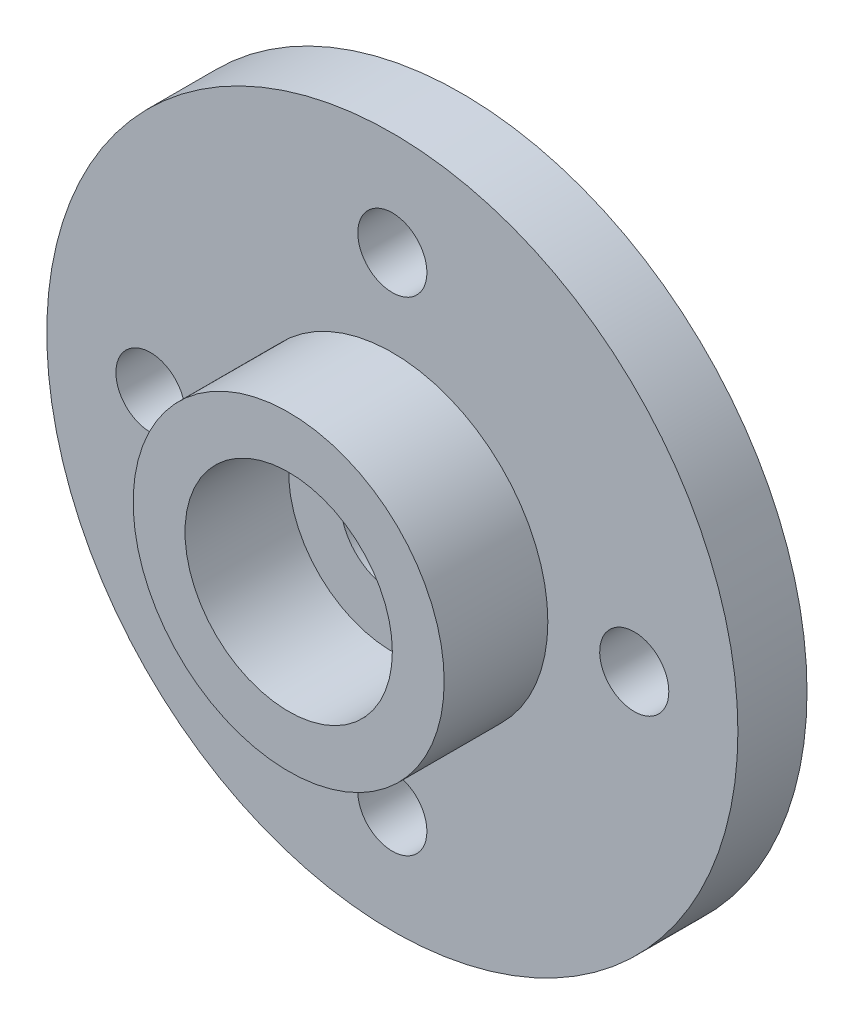
SolidWorks part; units mm, degrees
ref_plane "Front Plane" through (0, 0, 0) normal (0, 0, 1) x (1, 0, 0)
ref_plane "Top Plane" through (0, 0, 0) normal (0, 1, 0) x (1, 0, 0)
ref_plane "Right Plane" through (0, 0, 0) normal (1, 0, 0) x (0, 0, -1)
sketch "Sketch1" plane through (0, 0, 0) normal (0, 0, 1) x (1, 0, 0)
  circle A0 centre (0, 0) radius 10
  circle A1 centre (0, 0) radius 1.5
  dimension "D1" = 20
  dimension "D2" = 3
extrude "Boss-Extrude1" add sketch "Sketch1" along normal blind 2
sketch "Sketch2" plane through (0, 0, 2) normal (0, 0, 1) x (1, 0, 0)
  circle A0 centre (0, 0) radius 4.5
  circle A1 centre (0, 0) radius 3
  dimension "D1" = 9
  dimension "D2" = 6
extrude "Boss-Extrude2" add sketch "Sketch2" along normal blind 3
sketch "Sketch3" plane through (0, 0, 0) normal (0, 0, -1) x (-1, 0, 0)
  circle A0 centre (0, 0) radius 7 construction
  circle A1 centre (0, 7) radius 1
  dimension "D1" = 14
  dimension "D2" = 2
extrude "Cut-Extrude1" cut sketch "Sketch3" against normal up to surface (2 mm away) up to face at (4.5, 0, 2)
pattern_circular "CirPattern1" count 4 over 360 about axis through (0, 0, 0) along (0, 0, 1) of "Cut-Extrude1"
